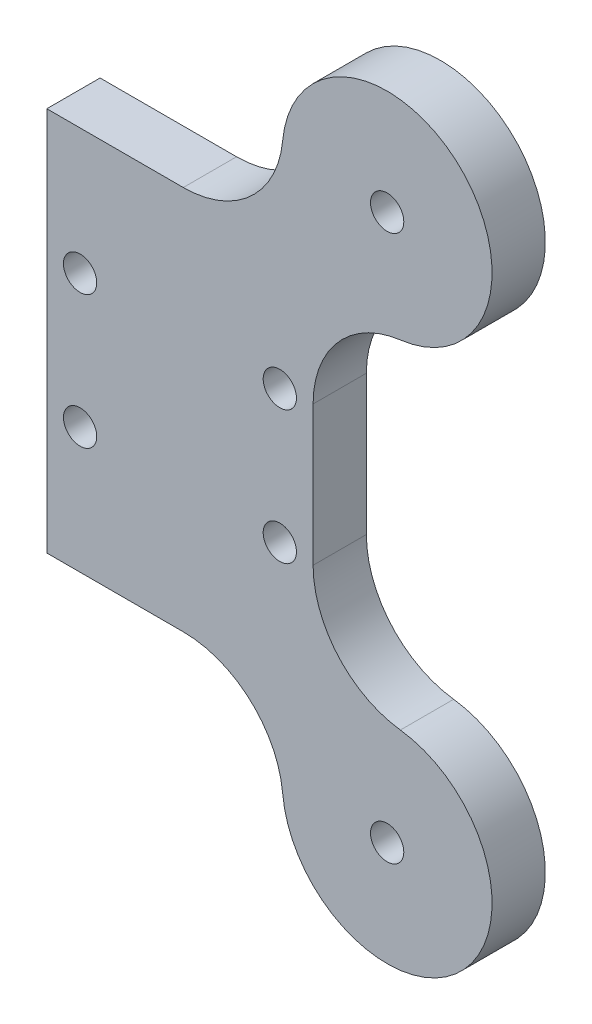
SolidWorks part; units mm, degrees
ref_plane "Front Plane" through (0, 0, 0) normal (0, 0, 1) x (1, 0, 0)
ref_plane "Top Plane" through (0, 0, 0) normal (0, 1, 0) x (1, 0, 0)
ref_plane "Right Plane" through (0, 0, 0) normal (1, 0, 0) x (0, 0, -1)
sketch "Sketch1" plane through (0, 0, 0) normal (0, 0, 1) x (1, 0, 0)
  line L2 (-10, -14.45) -> (7.681, -14.45)
  line L3 (7.681, -20.5023) -> (7.681, -14.45)
  line L4 (-10, 0) -> (-10, -14.45)
  line L5 (10, 0) -> (10, -12.6223)
  line L6 (-10, 0) -> (10, 0)
  line L7 (15.561, -12.6223) -> (10, -12.6223)
  arc A3 (7.681, -20.5023) -> (15.561, -12.6223) centre (15.561, -20.5023) ccw
  circle A4 centre (-7.5, -5) radius 1.25
  circle A5 centre (7.5, -5) radius 1.25
  circle A6 centre (15.561, -20.5023) radius 1.25
  dimension "D1" = 2.5
extrude "Boss-Extrude1" add sketch "Sketch1" along normal blind 4 contours A4 | A6 | L4 L2 L3 A3 L7 L5 L6 | A5
fillet "Fillet1" radius 7.5 2 edges at (7.681, -14.45, 2) (10, -12.6223, 2)
mirror "Mirror1" about plane through (-10, 0, 4) normal (0, 1, 0) of "Boss-Extrude1", "Fillet1"
